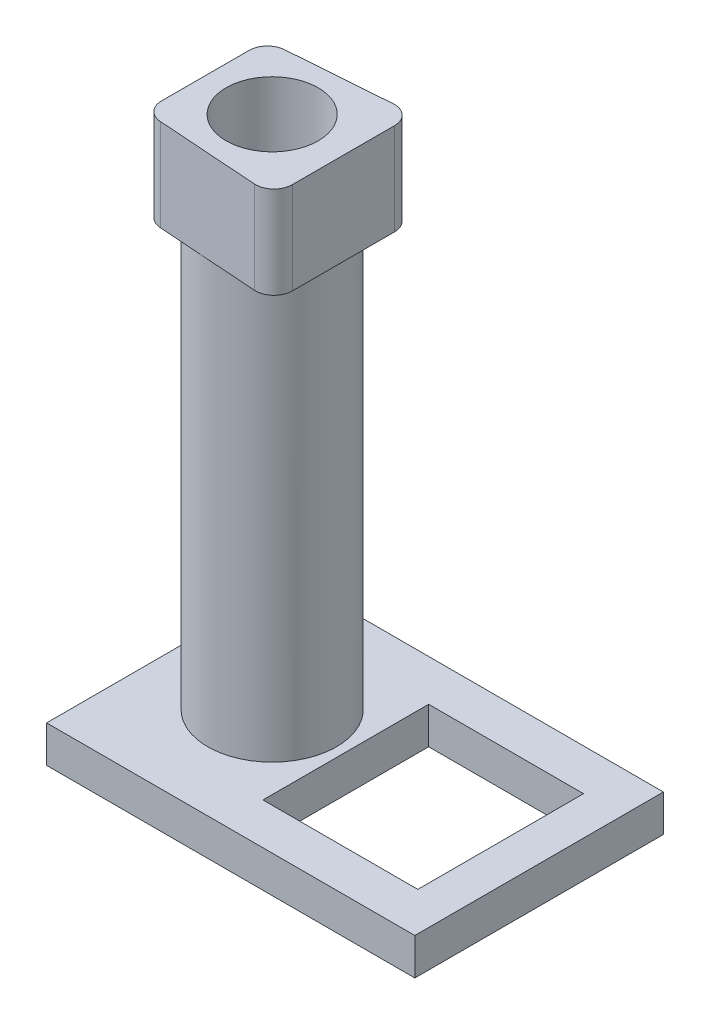
SolidWorks part; units mm, degrees
ref_plane "Спереди" through (0, 0, 0) normal (0, 0, 1) x (1, 0, 0)
ref_plane "Сверху" through (0, 0, 0) normal (0, 1, 0) x (1, 0, 0)
ref_plane "Справа" through (0, 0, 0) normal (1, 0, 0) x (0, 0, -1)
sketch "Эскиз1" plane through (0, 0, 0) normal (0, 1, 0) x (1, 0, 0)
  line L0 (-12.3747, 0) -> (66.873, 0) construction
  line L1 (-55, -67.5) -> (145, -67.5)
  line L2 (-55, -67.5) -> (-55, 67.5)
  line L3 (-55, 67.5) -> (145, 67.5)
  line L4 (145, -67.5) -> (145, 67.5)
  line L5 (-55, -67.5) -> (145, 67.5) construction
  line L6 (-55, 67.5) -> (145, -67.5) construction
  line L7 (40, -45) -> (124.1121, -45)
  line L8 (40, -45) -> (40, 45)
  line L9 (40, 45) -> (124.1121, 45)
  line L10 (124.1121, -45) -> (124.1121, 45)
  point P0 (45, 0)
  point P10 (40, 0)
extrude "Бобышка-Вытянуть1" add sketch "Эскиз1" along normal blind 20
sketch "Эскиз3" plane through (0, 20, 0) normal (0, 1, 0) x (1, 0, 0)
  circle A0 centre (0, 0) radius 35
extrude "Вытянуть-Тонкостенный1" add sketch "Эскиз3" along normal blind 230 thin thin type one direction reverse wall 10
sketch "Эскиз4" plane through (0, 250, 0) normal (0, 1, 0) x (1, 0, 0)
  line L1 (38.567, 27.8805) -> (38.567, -27.6017)
  line L2 (27.8707, -37.5774) -> (-27.0249, -33.7454)
  line L3 (-27.0732, 33.7534) -> (27.8224, 37.8528)
  line L4 (-36.3285, -23.7697) -> (-36.3285, 23.7812)
  arc A0 (-36.3285, -23.7697) -> (-27.0249, -33.7454) centre (-26.3285, -23.7697) ccw
  arc A1 (38.567, -27.6017) -> (27.8707, -37.5774) centre (28.567, -27.6017) cw
  arc A2 (27.8224, 37.8528) -> (38.567, 27.8805) centre (28.567, 27.8805) cw
  arc A3 (-36.3285, 23.7812) -> (-27.0732, 33.7534) centre (-26.3285, 23.7812) cw
  circle A4 centre (0, 0) radius 25
  dimension "D1" = 10
  dimension "D2" = 10
extrude "Бобышка-Вытянуть2" add sketch "Эскиз4" along normal blind 50
